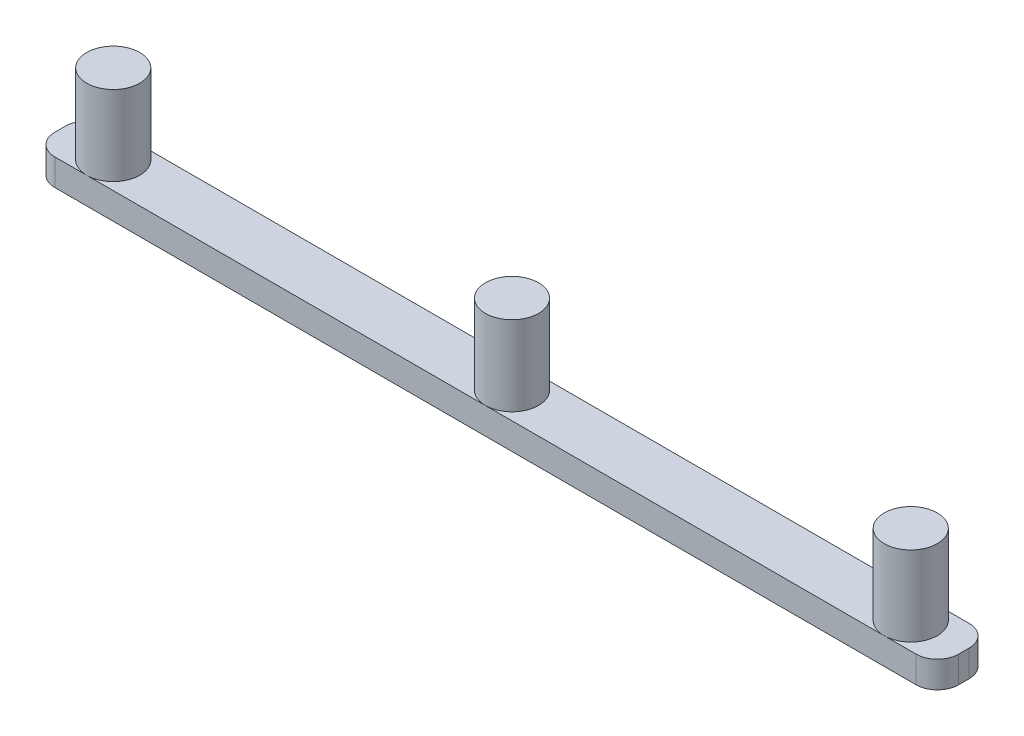
SolidWorks part; units mm, degrees
ref_plane "Plan de face" through (0, 0, 0) normal (0, 0, 1) x (1, 0, 0)
ref_plane "Plan de dessus" through (0, 0, 0) normal (0, 1, 0) x (1, 0, 0)
ref_plane "Plan de droite" through (0, 0, 0) normal (1, 0, 0) x (0, 0, -1)
sketch "Esquisse1" plane through (0, 0, 0) normal (0, 1, 0) x (1, 0, 0)
  line L1 (-4, 0) -> (-166, 0)
  line L2 (0, 4) -> (0, 6)
  line L3 (-4, 10) -> (-166, 10)
  line L4 (-170, 4) -> (-170, 6)
  arc A0 (0, 6) -> (-4, 10) centre (-4, 6) ccw
  arc A1 (0, 4) -> (-4, 0) centre (-4, 4) cw
  arc A2 (-166, 0) -> (-170, 4) centre (-166, 4) cw
  arc A3 (-170, 6) -> (-166, 10) centre (-166, 6) cw
  point P7 (0, 10)
  point P10 (0, 0)
  point P13 (-170, 0)
  dimension "D3" = 4
  dimension "D1" = 170
  dimension "D2" = 10
extrude "Boss.-Extru.1" add sketch "Esquisse1" along normal blind 5
sketch "Esquisse2" plane through (0, 5, 0) normal (0, 1, 0) x (1, 0, 0)
  line L0 (-170, 5) -> (0, 5) construction
  line L1 (-170, 6) -> (-170, 4) construction
  line L2 (0, 4) -> (0, 6) construction
  circle A0 centre (-160, 5) radius 5
  circle A1 centre (-85, 5) radius 5
  circle A2 centre (-10, 5) radius 5
  dimension "D1" = 85
  dimension "D2" = 10
  dimension "D3" = 10
  dimension "D4" = 10
  dimension "D5" = 10
  dimension "D6" = 10
extrude "Boss.-Extru.2" add sketch "Esquisse2" along normal blind 15
